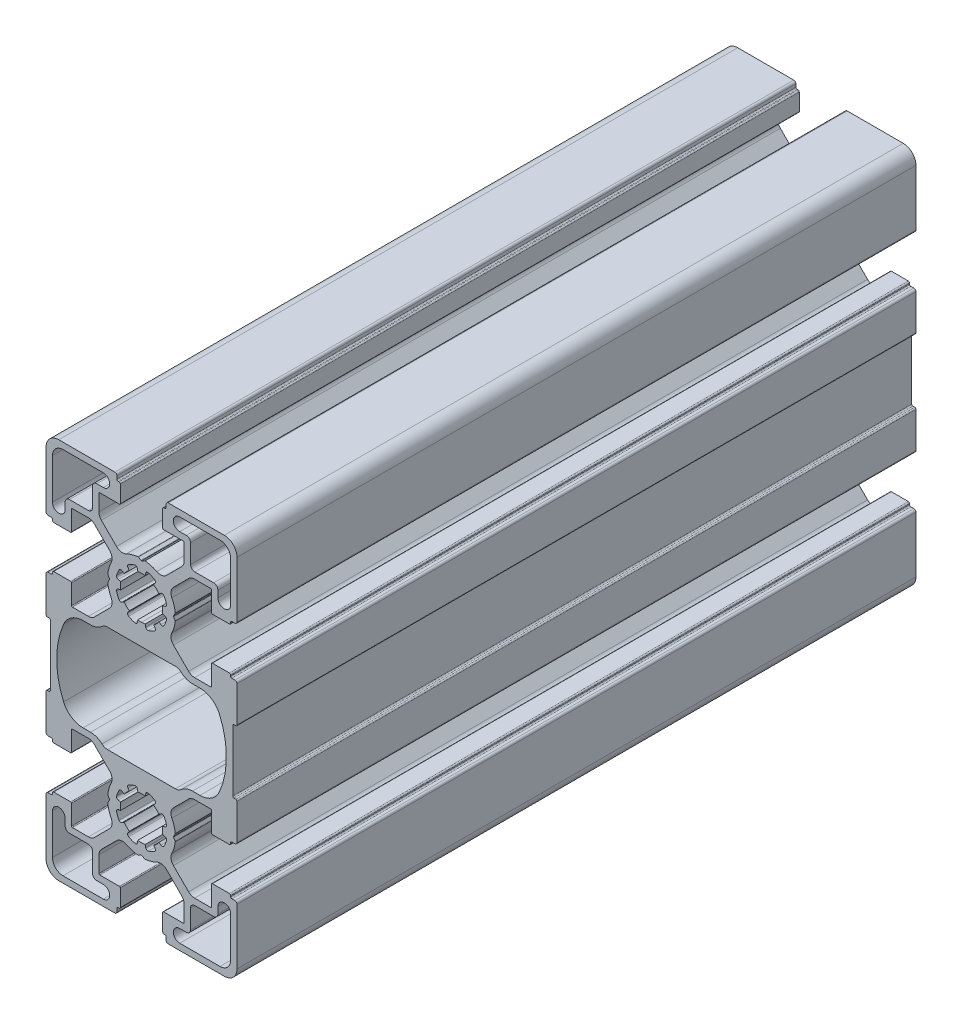
SolidWorks part; units mm, degrees
ref_plane "Front Plane" through (0, 0, 0) normal (0, 0, 1) x (1, 0, 0)
ref_plane "Top Plane" through (0, 0, 0) normal (0, 1, 0) x (1, 0, 0)
ref_plane "Right Plane" through (0, 0, 0) normal (1, 0, 0) x (0, 0, -1)
sketch "Sketch1" plane through (0, 0, 0) normal (0, 0, 1) x (1, 0, 0)
  line L0 (-17, 34.05) -> (-12.55, 34.05)
  line L1 (-18, 31.5) -> (-18, 33.05)
  line L2 (-21, 31.5) -> (-21, 41)
  line L3 (-18.5, 43.5) -> (-8.9998, 43.5)
  line L4 (-10.55, 40.5) -> (-8.9998, 40.5)
  line L5 (-11.55, 35.05) -> (-11.55, 39.5)
  line L6 (-13.7694, -10.95) -> (-12.0047, -10.95)
  line L7 (-7.9801, -12.5) -> (7.9801, -12.5)
  line L8 (-0.9685, -17.0071) -> (-0.8682, -17.576)
  line L9 (-3.1992, -17.9311) -> (-2.8679, -18.4042)
  line L10 (-4.5689, -19.3008) -> (-4.0957, -19.6321)
  line L11 (-5.4929, -21.5315) -> (-4.924, -21.6318)
  line L12 (-0.7408, 30.4278) -> (-0.1028, 30.0594)
  line L13 (-5.4929, -23.4686) -> (-4.924, -23.3683)
  line L14 (-4.0957, -25.3679) -> (-4.5689, -25.6992)
  line L15 (-3.1992, -27.0689) -> (-2.8679, -26.5958)
  line L16 (-0.8682, -27.424) -> (-0.9685, -27.9929)
  line L17 (-9.4642, -33.5905) -> (-5.8979, -30.0242)
  line L18 (-10.05, -35.0048) -> (-10.05, -38.8)
  line L19 (-5.2, -39) -> (-9.85, -39)
  line L20 (-5, -39.2) -> (-5, -43.2)
  line L21 (-5.4999, -43.5) -> (-5.3, -43.5)
  line L22 (-5.7999, -43.8) -> (-5.7999, -44.5)
  line L23 (-19.5, -45) -> (-6.2999, -45)
  line L24 (-22.5, -28.8) -> (-22.5, -42)
  line L25 (-22, -28.3) -> (-21.2999, -28.3)
  line L26 (-20.9999, -27.8) -> (-20.9999, -28)
  line L27 (-20.6999, -27.5) -> (-16.6999, -27.5)
  line L28 (-16.4999, -27.7) -> (-16.4999, -32.35)
  line L29 (-16.2999, -32.55) -> (-12.5047, -32.55)
  line L30 (-7.5242, -28.3979) -> (-11.0905, -31.9642)
  line L31 (-7.5577, -22.6) -> (-7.9277, -23.2409)
  line L32 (-7.9277, -21.7591) -> (-7.5577, -22.4)
  line L33 (-11.0905, -13.0358) -> (-7.5242, -16.6021)
  line L34 (-16.2999, -12.45) -> (-12.5047, -12.45)
  line L35 (-16.4999, -12.65) -> (-16.4999, -17.3)
  line L36 (-20.6999, -17.5) -> (-16.6999, -17.5)
  line L37 (-20.9999, -17) -> (-20.9999, -17.2)
  line L38 (-22, -16.7) -> (-21.2999, -16.7)
  line L39 (-22.5, -7.8) -> (-22.5, -16.2)
  line L40 (-22.2, -7.5) -> (-21.8, -7.5)
  line L41 (-0.7408, -30.4278) -> (-0.1028, -30.0594)
  line L42 (-11.55, -35.05) -> (-11.55, -39.5)
  line L43 (-10.55, -40.5) -> (-8.9998, -40.5)
  line L44 (-18.5, -43.5) -> (-8.9998, -43.5)
  line L45 (-21, -31.5) -> (-21, -41)
  line L46 (-18, -31.5) -> (-18, -33.05)
  line L47 (-17, -34.05) -> (-12.55, -34.05)
  line L48 (13.7694, 10.95) -> (12.0047, 10.95)
  line L49 (0.9685, 17.0071) -> (0.8682, 17.576)
  line L50 (3.1992, 17.9311) -> (2.8679, 18.4042)
  line L51 (4.5689, 19.3008) -> (4.0957, 19.6321)
  line L52 (5.4929, 21.5315) -> (4.924, 21.6318)
  line L53 (5.4929, 23.4686) -> (4.924, 23.3683)
  line L54 (4.0957, 25.3679) -> (4.5689, 25.6992)
  line L55 (3.1992, 27.0689) -> (2.8679, 26.5958)
  line L56 (0.8682, 27.424) -> (0.9685, 27.9929)
  line L57 (9.4642, 33.5905) -> (5.8979, 30.0242)
  line L58 (10.05, 35.0048) -> (10.05, 38.8)
  line L59 (5.2, 39) -> (9.85, 39)
  line L60 (5, 39.2) -> (5, 43.2)
  line L61 (5.4999, 43.5) -> (5.3, 43.5)
  line L62 (5.7999, 43.8) -> (5.7999, 44.5)
  line L63 (19.5, 45) -> (6.2999, 45)
  line L64 (22.5, 28.8) -> (22.5, 42)
  line L65 (22, 28.3) -> (21.2999, 28.3)
  line L66 (20.9999, 27.8) -> (20.9999, 28)
  line L67 (20.6999, 27.5) -> (16.6999, 27.5)
  line L68 (16.4999, 27.7) -> (16.4999, 32.35)
  line L69 (16.2999, 32.55) -> (12.5047, 32.55)
  line L70 (7.5242, 28.3979) -> (11.0905, 31.9642)
  line L71 (7.5577, 22.6) -> (7.9277, 23.2409)
  line L72 (7.9277, 21.7591) -> (7.5577, 22.4)
  line L73 (11.0905, 13.0358) -> (7.5242, 16.6021)
  line L74 (16.2999, 12.45) -> (12.5047, 12.45)
  line L75 (16.4999, 12.65) -> (16.4999, 17.3)
  line L76 (20.6999, 17.5) -> (16.6999, 17.5)
  line L77 (20.9999, 17) -> (20.9999, 17.2)
  line L78 (22, 16.7) -> (21.2999, 16.7)
  line L79 (22.5, 7.8) -> (22.5, 16.2)
  line L80 (22.2, 7.5) -> (21.8, 7.5)
  line L81 (21.5, -7.2) -> (21.5, 7.2)
  line L82 (17, -34.05) -> (12.55, -34.05)
  line L83 (18, -31.5) -> (18, -33.05)
  line L84 (21, -31.5) -> (21, -41)
  line L85 (18.5, -43.5) -> (8.9998, -43.5)
  line L86 (10.55, -40.5) -> (8.9998, -40.5)
  line L87 (11.55, -35.05) -> (11.55, -39.5)
  line L88 (0.7408, -30.4278) -> (0.1028, -30.0594)
  line L89 (-21.5, -7.2) -> (-21.5, 7.2)
  line L90 (-22.2, 7.5) -> (-21.8, 7.5)
  line L91 (-22.5, 7.8) -> (-22.5, 16.2)
  line L92 (-22, 16.7) -> (-21.2999, 16.7)
  line L93 (-20.9999, 17) -> (-20.9999, 17.2)
  line L94 (-20.6999, 17.5) -> (-16.6999, 17.5)
  line L95 (-16.4999, 12.65) -> (-16.4999, 17.3)
  line L96 (-16.2999, 12.45) -> (-12.5047, 12.45)
  line L97 (-11.0905, 13.0358) -> (-7.5242, 16.6021)
  line L98 (-7.9277, 21.7591) -> (-7.5577, 22.4)
  line L99 (-7.5577, 22.6) -> (-7.9277, 23.2409)
  line L100 (-7.5242, 28.3979) -> (-11.0905, 31.9642)
  line L101 (-16.2999, 32.55) -> (-12.5047, 32.55)
  line L102 (-16.4999, 27.7) -> (-16.4999, 32.35)
  line L103 (-20.6999, 27.5) -> (-16.6999, 27.5)
  line L104 (-20.9999, 27.8) -> (-20.9999, 28)
  line L105 (-22, 28.3) -> (-21.2999, 28.3)
  line L106 (-22.5, 28.8) -> (-22.5, 42)
  line L107 (-19.5, 45) -> (-6.2999, 45)
  line L108 (-5.7999, 43.8) -> (-5.7999, 44.5)
  line L109 (-5.4999, 43.5) -> (-5.3, 43.5)
  line L110 (-5, 39.2) -> (-5, 43.2)
  line L111 (-5.2, 39) -> (-9.85, 39)
  line L112 (-10.05, 35.0048) -> (-10.05, 38.8)
  line L113 (-9.4642, 33.5905) -> (-5.8979, 30.0242)
  line L114 (22.2, -7.5) -> (21.8, -7.5)
  line L115 (22.5, -7.8) -> (22.5, -16.2)
  line L116 (22, -16.7) -> (21.2999, -16.7)
  line L117 (20.9999, -17) -> (20.9999, -17.2)
  line L118 (20.6999, -17.5) -> (16.6999, -17.5)
  line L119 (16.4999, -12.65) -> (16.4999, -17.3)
  line L120 (16.2999, -12.45) -> (12.5047, -12.45)
  line L121 (11.0905, -13.0358) -> (7.5242, -16.6021)
  line L122 (7.9277, -21.7591) -> (7.5577, -22.4)
  line L123 (7.5577, -22.6) -> (7.9277, -23.2409)
  line L124 (7.5242, -28.3979) -> (11.0905, -31.9642)
  line L125 (16.2999, -32.55) -> (12.5047, -32.55)
  line L126 (16.4999, -27.7) -> (16.4999, -32.35)
  line L127 (20.6999, -27.5) -> (16.6999, -27.5)
  line L128 (20.9999, -27.8) -> (20.9999, -28)
  line L129 (22, -28.3) -> (21.2999, -28.3)
  line L130 (22.5, -28.8) -> (22.5, -42)
  line L131 (19.5, -45) -> (6.2999, -45)
  line L132 (5.7999, -43.8) -> (5.7999, -44.5)
  line L133 (5.4999, -43.5) -> (5.3, -43.5)
  line L134 (5, -39.2) -> (5, -43.2)
  line L135 (5.2, -39) -> (9.85, -39)
  line L136 (10.05, -35.0048) -> (10.05, -38.8)
  line L137 (9.4642, -33.5905) -> (5.8979, -30.0242)
  line L138 (0.8682, -27.424) -> (0.9685, -27.9929)
  line L139 (3.1992, -27.0689) -> (2.8679, -26.5958)
  line L140 (4.0957, -25.3679) -> (4.5689, -25.6992)
  line L141 (5.4929, -23.4686) -> (4.924, -23.3683)
  line L142 (0.7408, 30.4278) -> (0.1028, 30.0594)
  line L143 (5.4929, -21.5315) -> (4.924, -21.6318)
  line L144 (4.5689, -19.3008) -> (4.0957, -19.6321)
  line L145 (3.1992, -17.9311) -> (2.8679, -18.4042)
  line L146 (0.9685, -17.0071) -> (0.8682, -17.576)
  line L147 (13.7694, -10.95) -> (12.0047, -10.95)
  line L148 (-0.8682, 27.424) -> (-0.9685, 27.9929)
  line L149 (-3.1992, 27.0689) -> (-2.8679, 26.5958)
  line L150 (-4.0957, 25.3679) -> (-4.5689, 25.6992)
  line L151 (-5.4929, 23.4686) -> (-4.924, 23.3683)
  line L152 (-5.4929, 21.5315) -> (-4.924, 21.6318)
  line L153 (-4.5689, 19.3008) -> (-4.0957, 19.6321)
  line L154 (-3.1992, 17.9311) -> (-2.8679, 18.4042)
  line L155 (-0.9685, 17.0071) -> (-0.8682, 17.576)
  line L156 (11.55, 35.05) -> (11.55, 39.5)
  line L157 (10.55, 40.5) -> (8.9998, 40.5)
  line L158 (18.5, 43.5) -> (8.9998, 43.5)
  line L159 (21, 31.5) -> (21, 41)
  line L160 (-7.9801, 12.5) -> (7.9801, 12.5)
  line L161 (-13.7694, 10.95) -> (-12.0047, 10.95)
  line L162 (18, 31.5) -> (18, 33.05)
  line L163 (17, 34.05) -> (12.55, 34.05)
  line L164 (-43.0349, 0) -> (65.7175, 0) construction
  line L165 (0.0001, 22.5) -> (42.6876, 22.5) construction
  line L166 (0, 22.5) -> (-43.0349, 22.5) construction
  line L167 (0, 54.8172) -> (0, -53.1422) construction
  line L168 (0, -22.5) -> (47.5631, -22.5) construction
  line L169 (-0.0001, -22.5) -> (-41.4143, -22.5) construction
  line L170 (-1.5914, -30.5) -> (1.5914, -30.5) construction
  arc A0 (-12.55, 34.05) -> (-11.55, 35.05) centre (-12.55, 35.05) ccw
  arc A1 (-17, 34.05) -> (-18, 33.05) centre (-17, 33.05) ccw
  arc A2 (-21, 31.5) -> (-18, 31.5) centre (-19.5, 31.5) ccw
  arc A3 (-18.5, 43.5) -> (-21, 41) centre (-18.5, 41) ccw
  arc A4 (-8.9998, 40.5) -> (-8.9998, 43.5) centre (-8.9998, 42) ccw
  arc A5 (-10.55, 40.5) -> (-11.55, 39.5) centre (-10.55, 39.5) ccw
  arc A6 (-13.7694, -10.95) -> (-18.3592, -7.9333) centre (-13.7694, -5.95) cw
  arc A7 (-12.0047, -10.95) -> (-9.3217, -11.9833) centre (-12.0047, -14.95) cw
  arc A8 (-7.9801, -12.5) -> (-9.3217, -11.9833) centre (-7.9801, -10.5) cw
  arc A9 (-0.8682, -17.576) -> (0, -17.5) centre (0, -22.5) cw
  arc A10 (-1.5914, -16.6112) -> (-0.9685, -17.0071) centre (-1.4609, -17.0939) cw
  arc A11 (-3.0387, -17.2107) -> (-1.5914, -16.6112) centre (0, -22.5) cw
  arc A12 (-0.7408, 30.4278) -> (-0.8624, 30.4534) centre (-0.8408, 30.2546) ccw
  arc A13 (-0.1028, 30.0594) -> (0, 30.0309) centre (0, 30.2309) ccw
  arc A14 (-3.1992, -17.9311) -> (-3.0387, -17.2107) centre (-2.7896, -17.6443) cw
  arc A15 (-4.0957, -19.6321) -> (-2.8679, -18.4042) centre (0, -22.5) cw
  arc A16 (-5.2892, -19.4613) -> (-4.5689, -19.3008) centre (-4.8557, -19.7104) cw
  arc A17 (-5.8887, -20.9086) -> (-5.2892, -19.4613) centre (0.0001, -22.5) cw
  arc A18 (-5.4929, -21.5315) -> (-5.8887, -20.9086) centre (-5.406, -21.0391) cw
  arc A19 (-4.924, -23.3683) -> (-4.924, -21.6318) centre (0, -22.5) cw
  arc A20 (-5.8887, -24.0914) -> (-5.4929, -23.4686) centre (-5.406, -23.961) cw
  arc A21 (-5.2892, -25.5387) -> (-5.8887, -24.0914) centre (0, -22.5) cw
  arc A22 (-4.5689, -25.6992) -> (-5.2892, -25.5387) centre (-4.8557, -25.2896) cw
  arc A23 (-2.8679, -26.5958) -> (-4.0957, -25.3679) centre (0, -22.5) cw
  arc A24 (-3.0387, -27.7893) -> (-3.1992, -27.0689) centre (-2.7896, -27.3557) cw
  arc A25 (-1.5914, -28.3888) -> (-3.0387, -27.7893) centre (0.0001, -22.5) cw
  arc A26 (-0.9685, -27.9929) -> (-1.5914, -28.3888) centre (-1.4609, -27.9061) cw
  arc A27 (0.8682, -27.424) -> (-0.8682, -27.424) centre (0, -22.5) cw
  arc A28 (-0.8624, -30.4534) -> (-3.5869, -29.6508) centre (0, -22.5) cw
  arc A29 (-5.8979, -30.0242) -> (-3.5869, -29.6508) centre (-4.4837, -31.4385) cw
  arc A30 (-10.05, -35.0048) -> (-9.4642, -33.5905) centre (-8.0499, -35.0048) cw
  arc A31 (-9.85, -39) -> (-10.05, -38.8) centre (-9.85, -38.8) cw
  arc A32 (-5.2, -39) -> (-5, -39.2) centre (-5.2, -39.2) cw
  arc A33 (-5, -43.2) -> (-5.3, -43.5) centre (-5.3, -43.2) cw
  arc A34 (-5.7999, -43.8) -> (-5.4999, -43.5) centre (-5.4999, -43.8) cw
  arc A35 (-5.7999, -44.5) -> (-6.2999, -45) centre (-6.2999, -44.5) cw
  arc A36 (-19.5, -45) -> (-22.5, -42) centre (-19.5, -42) cw
  arc A37 (-22.5, -28.8) -> (-22, -28.3) centre (-22, -28.8) cw
  arc A38 (-20.9999, -28) -> (-21.2999, -28.3) centre (-21.2999, -28) cw
  arc A39 (-20.9999, -27.8) -> (-20.6999, -27.5) centre (-20.6999, -27.8) cw
  arc A40 (-16.6999, -27.5) -> (-16.4999, -27.7) centre (-16.6999, -27.7) cw
  arc A41 (-16.2999, -32.55) -> (-16.4999, -32.35) centre (-16.2999, -32.35) cw
  arc A42 (-11.0905, -31.9642) -> (-12.5047, -32.55) centre (-12.5047, -30.55) cw
  arc A43 (-7.1507, -26.087) -> (-7.5242, -28.3979) centre (-8.9384, -26.9837) cw
  arc A44 (-7.1507, -26.087) -> (-7.9533, -23.3624) centre (0.0001, -22.5) cw
  arc A45 (-7.9533, -23.3624) -> (-7.9277, -23.2409) centre (-7.7545, -23.3409) cw
  arc A46 (-7.5577, -22.4) -> (-7.5577, -22.6) centre (-7.7309, -22.5) cw
  arc A47 (-7.9277, -21.7591) -> (-7.9533, -21.6376) centre (-7.7545, -21.6591) cw
  arc A48 (-7.9533, -21.6376) -> (-7.1507, -18.913) centre (0.0001, -22.5) cw
  arc A49 (-7.5242, -16.6021) -> (-7.1507, -18.913) centre (-8.9384, -18.0163) cw
  arc A50 (-12.5047, -12.45) -> (-11.0905, -13.0358) centre (-12.5047, -14.45) cw
  arc A51 (-16.4999, -12.65) -> (-16.2999, -12.45) centre (-16.2999, -12.65) cw
  arc A52 (-16.4999, -17.3) -> (-16.6999, -17.5) centre (-16.6999, -17.3) cw
  arc A53 (-20.6999, -17.5) -> (-20.9999, -17.2) centre (-20.6999, -17.2) cw
  arc A54 (-21.2999, -16.7) -> (-20.9999, -17) centre (-21.2999, -17) cw
  arc A55 (-22, -16.7) -> (-22.5, -16.2) centre (-22, -16.2) cw
  arc A56 (-22.5, -7.8) -> (-22.2, -7.5) centre (-22.2, -7.8) cw
  arc A57 (-21.5, -7.2) -> (-21.8, -7.5) centre (-21.8, -7.2) cw
  arc A58 (-0.1028, -30.0594) -> (0, -30.0309) centre (0, -30.2309) cw
  arc A59 (-0.7408, -30.4278) -> (-0.8624, -30.4534) centre (-0.8408, -30.2546) cw
  arc A60 (-10.55, -40.5) -> (-11.55, -39.5) centre (-10.55, -39.5) cw
  arc A61 (-8.9998, -40.5) -> (-8.9998, -43.5) centre (-8.9998, -42) cw
  arc A62 (-18.5, -43.5) -> (-21, -41) centre (-18.5, -41) cw
  arc A63 (-21, -31.5) -> (-18, -31.5) centre (-19.5, -31.5) cw
  arc A64 (-17, -34.05) -> (-18, -33.05) centre (-17, -33.05) cw
  arc A65 (-12.55, -34.05) -> (-11.55, -35.05) centre (-12.55, -35.05) cw
  arc A66 (18.3592, 7.9333) -> (18.3592, -7.9333) centre (0, 0) cw
  arc A67 (13.7694, 10.95) -> (18.3592, 7.9333) centre (13.7694, 5.95) cw
  arc A68 (12.0047, 10.95) -> (9.3217, 11.9833) centre (12.0047, 14.95) cw
  arc A69 (7.9801, 12.5) -> (9.3217, 11.9833) centre (7.9801, 10.5) cw
  arc A70 (0.8682, 17.576) -> (0, 17.5) centre (0, 22.5) cw
  arc A71 (1.5914, 16.6112) -> (0.9685, 17.0071) centre (1.4609, 17.0939) cw
  arc A72 (3.0387, 17.2107) -> (1.5914, 16.6112) centre (0, 22.5) cw
  arc A73 (3.1992, 17.9311) -> (3.0387, 17.2107) centre (2.7896, 17.6443) cw
  arc A74 (4.0957, 19.6321) -> (2.8679, 18.4042) centre (0, 22.5) cw
  arc A75 (5.2892, 19.4613) -> (4.5689, 19.3008) centre (4.8557, 19.7104) cw
  arc A76 (5.8887, 20.9086) -> (5.2892, 19.4613) centre (-0.0001, 22.5) cw
  arc A77 (5.4929, 21.5315) -> (5.8887, 20.9086) centre (5.406, 21.0391) cw
  arc A78 (4.924, 23.3683) -> (4.924, 21.6318) centre (0, 22.5) cw
  arc A79 (5.8887, 24.0914) -> (5.4929, 23.4686) centre (5.406, 23.961) cw
  arc A80 (5.2892, 25.5387) -> (5.8887, 24.0914) centre (0, 22.5) cw
  arc A81 (4.5689, 25.6992) -> (5.2892, 25.5387) centre (4.8557, 25.2896) cw
  arc A82 (2.8679, 26.5958) -> (4.0957, 25.3679) centre (0, 22.5) cw
  arc A83 (3.0387, 27.7893) -> (3.1992, 27.0689) centre (2.7896, 27.3557) cw
  arc A84 (1.5914, 28.3888) -> (3.0387, 27.7893) centre (-0.0001, 22.5) cw
  arc A85 (0.9685, 27.9929) -> (1.5914, 28.3888) centre (1.4609, 27.9061) cw
  arc A86 (0.8624, 30.4534) -> (3.5869, 29.6508) centre (0, 22.5) cw
  arc A87 (5.8979, 30.0242) -> (3.5869, 29.6508) centre (4.4837, 31.4385) cw
  arc A88 (10.05, 35.0048) -> (9.4642, 33.5905) centre (8.0499, 35.0048) cw
  arc A89 (9.85, 39) -> (10.05, 38.8) centre (9.85, 38.8) cw
  arc A90 (5.2, 39) -> (5, 39.2) centre (5.2, 39.2) cw
  arc A91 (5, 43.2) -> (5.3, 43.5) centre (5.3, 43.2) cw
  arc A92 (5.7999, 43.8) -> (5.4999, 43.5) centre (5.4999, 43.8) cw
  arc A93 (5.7999, 44.5) -> (6.2999, 45) centre (6.2999, 44.5) cw
  arc A94 (19.5, 45) -> (22.5, 42) centre (19.5, 42) cw
  arc A95 (22.5, 28.8) -> (22, 28.3) centre (22, 28.8) cw
  arc A96 (20.9999, 28) -> (21.2999, 28.3) centre (21.2999, 28) cw
  arc A97 (20.9999, 27.8) -> (20.6999, 27.5) centre (20.6999, 27.8) cw
  arc A98 (16.6999, 27.5) -> (16.4999, 27.7) centre (16.6999, 27.7) cw
  arc A99 (16.2999, 32.55) -> (16.4999, 32.35) centre (16.2999, 32.35) cw
  arc A100 (11.0905, 31.9642) -> (12.5047, 32.55) centre (12.5047, 30.55) cw
  arc A101 (7.1507, 26.087) -> (7.5242, 28.3979) centre (8.9384, 26.9837) cw
  arc A102 (7.1507, 26.087) -> (7.9533, 23.3624) centre (-0.0001, 22.5) cw
  arc A103 (7.9533, 23.3624) -> (7.9277, 23.2409) centre (7.7545, 23.3409) cw
  arc A104 (7.5577, 22.4) -> (7.5577, 22.6) centre (7.7309, 22.5) cw
  arc A105 (7.9277, 21.7591) -> (7.9533, 21.6376) centre (7.7545, 21.6591) cw
  arc A106 (7.9533, 21.6376) -> (7.1507, 18.913) centre (-0.0001, 22.5) cw
  arc A107 (7.5242, 16.6021) -> (7.1507, 18.913) centre (8.9384, 18.0163) cw
  arc A108 (-21.5, 7.2) -> (-21.8, 7.5) centre (-21.8, 7.2) ccw
  arc A109 (-22.5, 7.8) -> (-22.2, 7.5) centre (-22.2, 7.8) ccw
  arc A110 (-22, 16.7) -> (-22.5, 16.2) centre (-22, 16.2) ccw
  arc A111 (-21.2999, 16.7) -> (-20.9999, 17) centre (-21.2999, 17) ccw
  arc A112 (-20.6999, 17.5) -> (-20.9999, 17.2) centre (-20.6999, 17.2) ccw
  arc A113 (-16.4999, 17.3) -> (-16.6999, 17.5) centre (-16.6999, 17.3) ccw
  arc A114 (-16.4999, 12.65) -> (-16.2999, 12.45) centre (-16.2999, 12.65) ccw
  arc A115 (-12.5047, 12.45) -> (-11.0905, 13.0358) centre (-12.5047, 14.45) ccw
  arc A116 (-7.5242, 16.6021) -> (-7.1507, 18.913) centre (-8.9384, 18.0163) ccw
  arc A117 (-7.9533, 21.6376) -> (-7.1507, 18.913) centre (0.0001, 22.5) ccw
  arc A118 (-7.9277, 21.7591) -> (-7.9533, 21.6376) centre (-7.7545, 21.6591) ccw
  arc A119 (-7.5577, 22.4) -> (-7.5577, 22.6) centre (-7.7309, 22.5) ccw
  arc A120 (-7.9533, 23.3624) -> (-7.9277, 23.2409) centre (-7.7545, 23.3409) ccw
  arc A121 (-7.1507, 26.087) -> (-7.9533, 23.3624) centre (0.0001, 22.5) ccw
  arc A122 (-7.1507, 26.087) -> (-7.5242, 28.3979) centre (-8.9384, 26.9837) ccw
  arc A123 (-11.0905, 31.9642) -> (-12.5047, 32.55) centre (-12.5047, 30.55) ccw
  arc A124 (-16.2999, 32.55) -> (-16.4999, 32.35) centre (-16.2999, 32.35) ccw
  arc A125 (-16.6999, 27.5) -> (-16.4999, 27.7) centre (-16.6999, 27.7) ccw
  arc A126 (-20.9999, 27.8) -> (-20.6999, 27.5) centre (-20.6999, 27.8) ccw
  arc A127 (-20.9999, 28) -> (-21.2999, 28.3) centre (-21.2999, 28) ccw
  arc A128 (-22.5, 28.8) -> (-22, 28.3) centre (-22, 28.8) ccw
  arc A129 (-19.5, 45) -> (-22.5, 42) centre (-19.5, 42) ccw
  arc A130 (-5.7999, 44.5) -> (-6.2999, 45) centre (-6.2999, 44.5) ccw
  arc A131 (-5.7999, 43.8) -> (-5.4999, 43.5) centre (-5.4999, 43.8) ccw
  arc A132 (-5, 43.2) -> (-5.3, 43.5) centre (-5.3, 43.2) ccw
  arc A133 (-5.2, 39) -> (-5, 39.2) centre (-5.2, 39.2) ccw
  arc A134 (-9.85, 39) -> (-10.05, 38.8) centre (-9.85, 38.8) ccw
  arc A135 (-10.05, 35.0048) -> (-9.4642, 33.5905) centre (-8.0499, 35.0048) ccw
  arc A136 (-5.8979, 30.0242) -> (-3.5869, 29.6508) centre (-4.4837, 31.4385) ccw
  arc A137 (-0.8624, 30.4534) -> (-3.5869, 29.6508) centre (0, 22.5) ccw
  arc A138 (12.5047, 12.45) -> (11.0905, 13.0358) centre (12.5047, 14.45) cw
  arc A139 (16.4999, 12.65) -> (16.2999, 12.45) centre (16.2999, 12.65) cw
  arc A140 (16.4999, 17.3) -> (16.6999, 17.5) centre (16.6999, 17.3) cw
  arc A141 (20.6999, 17.5) -> (20.9999, 17.2) centre (20.6999, 17.2) cw
  arc A142 (21.2999, 16.7) -> (20.9999, 17) centre (21.2999, 17) cw
  arc A143 (22, 16.7) -> (22.5, 16.2) centre (22, 16.2) cw
  arc A144 (22.5, 7.8) -> (22.2, 7.5) centre (22.2, 7.8) cw
  arc A145 (21.5, 7.2) -> (21.8, 7.5) centre (21.8, 7.2) cw
  arc A146 (12.55, -34.05) -> (11.55, -35.05) centre (12.55, -35.05) ccw
  arc A147 (17, -34.05) -> (18, -33.05) centre (17, -33.05) ccw
  arc A148 (21, -31.5) -> (18, -31.5) centre (19.5, -31.5) ccw
  arc A149 (18.5, -43.5) -> (21, -41) centre (18.5, -41) ccw
  arc A150 (8.9998, -40.5) -> (8.9998, -43.5) centre (8.9998, -42) ccw
  arc A151 (10.55, -40.5) -> (11.55, -39.5) centre (10.55, -39.5) ccw
  arc A152 (0.7408, -30.4278) -> (0.8624, -30.4534) centre (0.8408, -30.2546) ccw
  arc A153 (0.1028, -30.0594) -> (0, -30.0309) centre (0, -30.2309) ccw
  arc A154 (21.5, -7.2) -> (21.8, -7.5) centre (21.8, -7.2) ccw
  arc A155 (22.5, -7.8) -> (22.2, -7.5) centre (22.2, -7.8) ccw
  arc A156 (22, -16.7) -> (22.5, -16.2) centre (22, -16.2) ccw
  arc A157 (21.2999, -16.7) -> (20.9999, -17) centre (21.2999, -17) ccw
  arc A158 (20.6999, -17.5) -> (20.9999, -17.2) centre (20.6999, -17.2) ccw
  arc A159 (16.4999, -17.3) -> (16.6999, -17.5) centre (16.6999, -17.3) ccw
  arc A160 (16.4999, -12.65) -> (16.2999, -12.45) centre (16.2999, -12.65) ccw
  arc A161 (12.5047, -12.45) -> (11.0905, -13.0358) centre (12.5047, -14.45) ccw
  arc A162 (7.5242, -16.6021) -> (7.1507, -18.913) centre (8.9384, -18.0163) ccw
  arc A163 (7.9533, -21.6376) -> (7.1507, -18.913) centre (-0.0001, -22.5) ccw
  arc A164 (7.9277, -21.7591) -> (7.9533, -21.6376) centre (7.7545, -21.6591) ccw
  arc A165 (7.5577, -22.4) -> (7.5577, -22.6) centre (7.7309, -22.5) ccw
  arc A166 (7.9533, -23.3624) -> (7.9277, -23.2409) centre (7.7545, -23.3409) ccw
  arc A167 (7.1507, -26.087) -> (7.9533, -23.3624) centre (-0.0001, -22.5) ccw
  arc A168 (7.1507, -26.087) -> (7.5242, -28.3979) centre (8.9384, -26.9837) ccw
  arc A169 (11.0905, -31.9642) -> (12.5047, -32.55) centre (12.5047, -30.55) ccw
  arc A170 (16.2999, -32.55) -> (16.4999, -32.35) centre (16.2999, -32.35) ccw
  arc A171 (16.6999, -27.5) -> (16.4999, -27.7) centre (16.6999, -27.7) ccw
  arc A172 (20.9999, -27.8) -> (20.6999, -27.5) centre (20.6999, -27.8) ccw
  arc A173 (20.9999, -28) -> (21.2999, -28.3) centre (21.2999, -28) ccw
  arc A174 (22.5, -28.8) -> (22, -28.3) centre (22, -28.8) ccw
  arc A175 (19.5, -45) -> (22.5, -42) centre (19.5, -42) ccw
  arc A176 (5.7999, -44.5) -> (6.2999, -45) centre (6.2999, -44.5) ccw
  arc A177 (5.7999, -43.8) -> (5.4999, -43.5) centre (5.4999, -43.8) ccw
  arc A178 (5, -43.2) -> (5.3, -43.5) centre (5.3, -43.2) ccw
  arc A179 (5.2, -39) -> (5, -39.2) centre (5.2, -39.2) ccw
  arc A180 (9.85, -39) -> (10.05, -38.8) centre (9.85, -38.8) ccw
  arc A181 (10.05, -35.0048) -> (9.4642, -33.5905) centre (8.0499, -35.0048) ccw
  arc A182 (5.8979, -30.0242) -> (3.5869, -29.6508) centre (4.4837, -31.4385) ccw
  arc A183 (0.8624, -30.4534) -> (3.5869, -29.6508) centre (0, -22.5) ccw
  arc A184 (0.9685, -27.9929) -> (1.5914, -28.3888) centre (1.4609, -27.9061) ccw
  arc A185 (1.5914, -28.3888) -> (3.0387, -27.7893) centre (-0.0001, -22.5) ccw
  arc A186 (3.0387, -27.7893) -> (3.1992, -27.0689) centre (2.7896, -27.3557) ccw
  arc A187 (2.8679, -26.5958) -> (4.0957, -25.3679) centre (0, -22.5) ccw
  arc A188 (4.5689, -25.6992) -> (5.2892, -25.5387) centre (4.8557, -25.2896) ccw
  arc A189 (5.2892, -25.5387) -> (5.8887, -24.0914) centre (0, -22.5) ccw
  arc A190 (5.8887, -24.0914) -> (5.4929, -23.4686) centre (5.406, -23.961) ccw
  arc A191 (4.924, -23.3683) -> (4.924, -21.6318) centre (0, -22.5) ccw
  arc A192 (5.4929, -21.5315) -> (5.8887, -20.9086) centre (5.406, -21.0391) ccw
  arc A193 (0.8682, 27.424) -> (-0.8682, 27.424) centre (0, 22.5) ccw
  arc A194 (-0.9685, 27.9929) -> (-1.5914, 28.3888) centre (-1.4609, 27.9061) ccw
  arc A195 (-1.5914, 28.3888) -> (-3.0387, 27.7893) centre (0.0001, 22.5) ccw
  arc A196 (-3.0387, 27.7893) -> (-3.1992, 27.0689) centre (-2.7896, 27.3557) ccw
  arc A197 (-2.8679, 26.5958) -> (-4.0957, 25.3679) centre (0, 22.5) ccw
  arc A198 (-4.5689, 25.6992) -> (-5.2892, 25.5387) centre (-4.8557, 25.2896) ccw
  arc A199 (-5.2892, 25.5387) -> (-5.8887, 24.0914) centre (0, 22.5) ccw
  arc A200 (-5.8887, 24.0914) -> (-5.4929, 23.4686) centre (-5.406, 23.961) ccw
  arc A201 (-4.924, 23.3683) -> (-4.924, 21.6318) centre (0, 22.5) ccw
  arc A202 (-5.4929, 21.5315) -> (-5.8887, 20.9086) centre (-5.406, 21.0391) ccw
  arc A203 (-5.8887, 20.9086) -> (-5.2892, 19.4613) centre (0.0001, 22.5) ccw
  arc A204 (-5.2892, 19.4613) -> (-4.5689, 19.3008) centre (-4.8557, 19.7104) ccw
  arc A205 (-4.0957, 19.6321) -> (-2.8679, 18.4042) centre (0, 22.5) ccw
  arc A206 (-3.1992, 17.9311) -> (-3.0387, 17.2107) centre (-2.7896, 17.6443) ccw
  arc A207 (-3.0387, 17.2107) -> (-1.5914, 16.6112) centre (0, 22.5) ccw
  arc A208 (-1.5914, 16.6112) -> (-0.9685, 17.0071) centre (-1.4609, 17.0939) ccw
  arc A209 (-0.8682, 17.576) -> (0, 17.5) centre (0, 22.5) ccw
  arc A210 (5.8887, -20.9086) -> (5.2892, -19.4613) centre (-0.0001, -22.5) ccw
  arc A211 (5.2892, -19.4613) -> (4.5689, -19.3008) centre (4.8557, -19.7104) ccw
  arc A212 (4.0957, -19.6321) -> (2.8679, -18.4042) centre (0, -22.5) ccw
  arc A213 (3.1992, -17.9311) -> (3.0387, -17.2107) centre (2.7896, -17.6443) ccw
  arc A214 (0.1028, 30.0594) -> (0, 30.0309) centre (0, 30.2309) cw
  arc A215 (0.7408, 30.4278) -> (0.8624, 30.4534) centre (0.8408, 30.2546) cw
  arc A216 (3.0387, -17.2107) -> (1.5914, -16.6112) centre (0, -22.5) ccw
  arc A217 (1.5914, -16.6112) -> (0.9685, -17.0071) centre (1.4609, -17.0939) ccw
  arc A218 (0.8682, -17.576) -> (0, -17.5) centre (0, -22.5) ccw
  arc A219 (7.9801, -12.5) -> (9.3217, -11.9833) centre (7.9801, -10.5) ccw
  arc A220 (12.0047, -10.95) -> (9.3217, -11.9833) centre (12.0047, -14.95) ccw
  arc A221 (-7.9801, 12.5) -> (-9.3217, 11.9833) centre (-7.9801, 10.5) ccw
  arc A222 (-12.0047, 10.95) -> (-9.3217, 11.9833) centre (-12.0047, 14.95) ccw
  arc A223 (-13.7694, 10.95) -> (-18.3592, 7.9333) centre (-13.7694, 5.95) ccw
  arc A224 (-18.3592, 7.9333) -> (-18.3592, -7.9333) centre (0, 0) ccw
  arc A225 (13.7694, -10.95) -> (18.3592, -7.9333) centre (13.7694, -5.95) ccw
  arc A226 (10.55, 40.5) -> (11.55, 39.5) centre (10.55, 39.5) cw
  arc A227 (8.9998, 40.5) -> (8.9998, 43.5) centre (8.9998, 42) cw
  arc A228 (18.5, 43.5) -> (21, 41) centre (18.5, 41) cw
  arc A229 (21, 31.5) -> (18, 31.5) centre (19.5, 31.5) cw
  arc A230 (17, 34.05) -> (18, 33.05) centre (17, 33.05) cw
  arc A231 (12.55, 34.05) -> (11.55, 35.05) centre (12.55, 35.05) cw
  point P219 (-21.5, 0)
  point P618 (21.5, 0)
  point P619 (0, 12.5)
  point P622 (0, -12.5)
  dimension "D7" = 10
  dimension "D1" = 9.9999
  dimension "D2" = 45
  dimension "D3" = 22.5001
  dimension "D4" = 90
  dimension "D5" = 22.5
  dimension "D6" = 14.5
  dimension "D8" = 44.9999
  dimension "D9" = 0.3
  dimension "D10" = 0.4
  dimension "D11" = 1
  dimension "D12" = 0.5
  dimension "D13" = 0.7
  dimension "D14" = 0.2
  dimension "D15" = 1.8
  dimension "D16" = 15
extrude "Base-Extrude" add sketch "Sketch1" against normal blind 160
